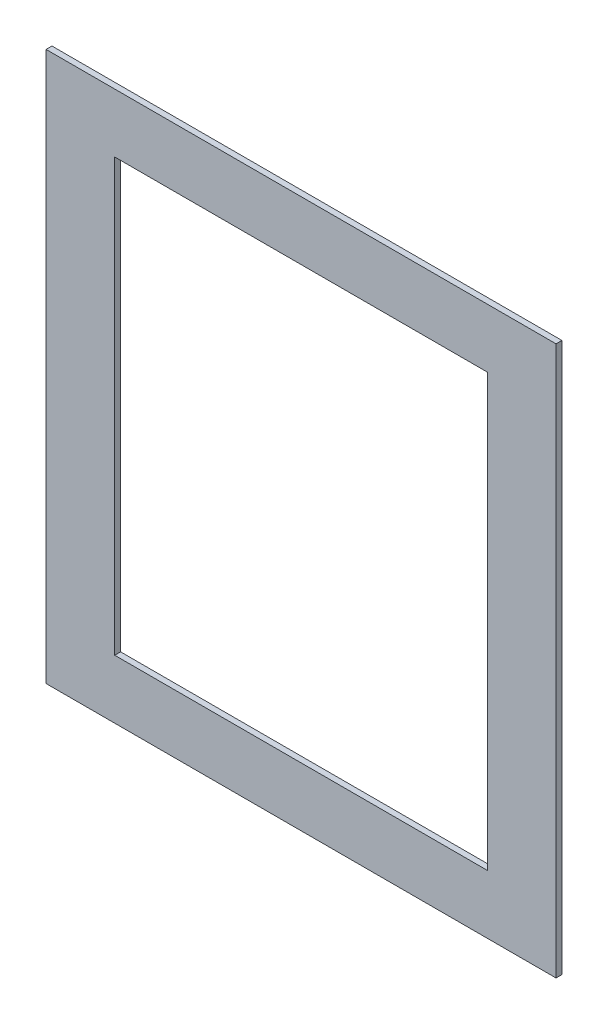
SolidWorks part; units mm, degrees
material "Клен"
ref_plane "Спереди" through (0, 0, 0) normal (0, 0, 1) x (1, 0, 0)
ref_plane "Сверху" through (0, 0, 0) normal (0, 1, 0) x (1, 0, 0)
ref_plane "Справа" through (0, 0, 0) normal (1, 0, 0) x (0, 0, -1)
sketch "Эскиз1" plane through (0, 0, 0) normal (0, 0, 1) x (1, 0, 0)
  line L0 (12.3279, 480.4642) -> (12.3279, 40.4642)
  line L1 (-57.6721, 540.4642) -> (462.3279, 540.4642)
  line L2 (-57.6721, 540.4642) -> (-57.6721, -19.5358)
  line L3 (-57.6721, -19.5358) -> (462.3279, -19.5358)
  line L4 (462.3279, 540.4642) -> (462.3279, -19.5358)
  line L5 (12.3279, 40.4642) -> (392.3279, 40.4642)
  line L6 (392.3279, 480.4642) -> (392.3279, 40.4642)
  line L7 (12.3279, 480.4642) -> (392.3279, 480.4642)
  point P8 (1210.7631, -316.166)
  point P9 (775.3324, -95.5751)
  point P10 (649.0305, 21.6249)
  point P11 (630.337, -182.6543)
  dimension "D1" = 60
  dimension "D2" = 500
  dimension "D3" = 60
  dimension "D4" = 380
  dimension "D5" = 70
  dimension "D6" = 70
extrude "Бобышка-Вытянуть1" add sketch "Эскиз1" along normal blind 6
equation "\"sheet_thickness\"= 6"
equation "\"D1@Бобышка-Вытянуть1\"= \"sheet_thickness\""
equation "\"bottom_line\"= 60"
equation "\"width_space\"= 500"
equation "\"D6@Эскиз1\"=\"D5@Эскиз1\""
